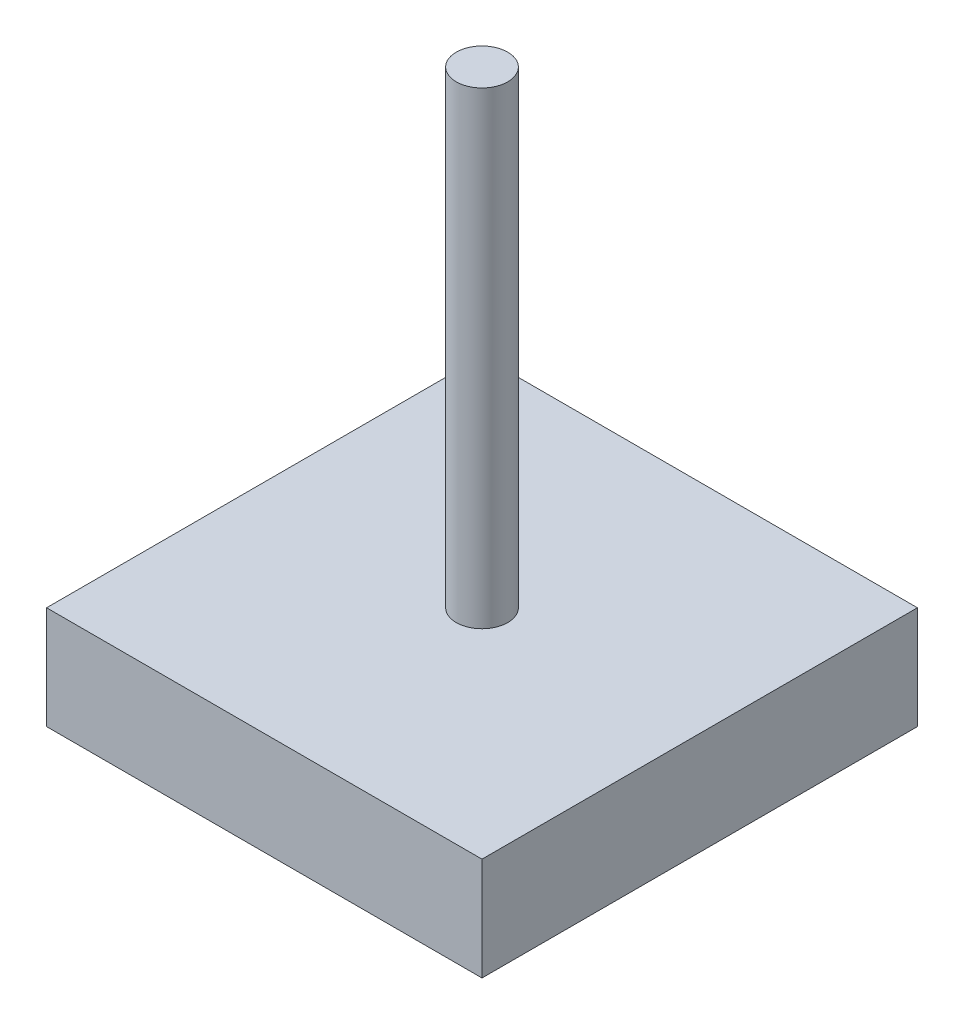
SolidWorks part; units mm, degrees
ref_plane "Front Plane" through (0, 0, 0) normal (0, 0, 1) x (1, 0, 0)
ref_plane "Top Plane" through (0, 0, 0) normal (0, 1, 0) x (1, 0, 0)
ref_plane "Right Plane" through (0, 0, 0) normal (1, 0, 0) x (0, 0, -1)
sketch "Sketch1" plane through (0, 0, 0) normal (0, 1, 0) x (1, 0, 0)
  line L1 (21.15, 21.15) -> (-21.15, 21.15)
  line L2 (21.15, 21.15) -> (21.15, -21.15)
  line L3 (21.15, -21.15) -> (-21.15, -21.15)
  line L4 (-21.15, 21.15) -> (-21.15, -21.15)
  line L5 (21.15, 21.15) -> (-21.15, -21.15) construction
  line L6 (21.15, -21.15) -> (-21.15, 21.15) construction
  point P0 (0, 0)
  dimension "D1" = 42.3
  dimension "D2" = 42.3
extrude "Boss-Extrude1" add sketch "Sketch1" along normal blind 10
sketch "Sketch2" plane through (0, 10, 0) normal (0, 1, 0) x (1, 0, 0)
  circle A0 centre (0, 0) radius 2.5
  dimension "D1" = 5
extrude "Boss-Extrude2" add sketch "Sketch2" along normal blind 45.5
